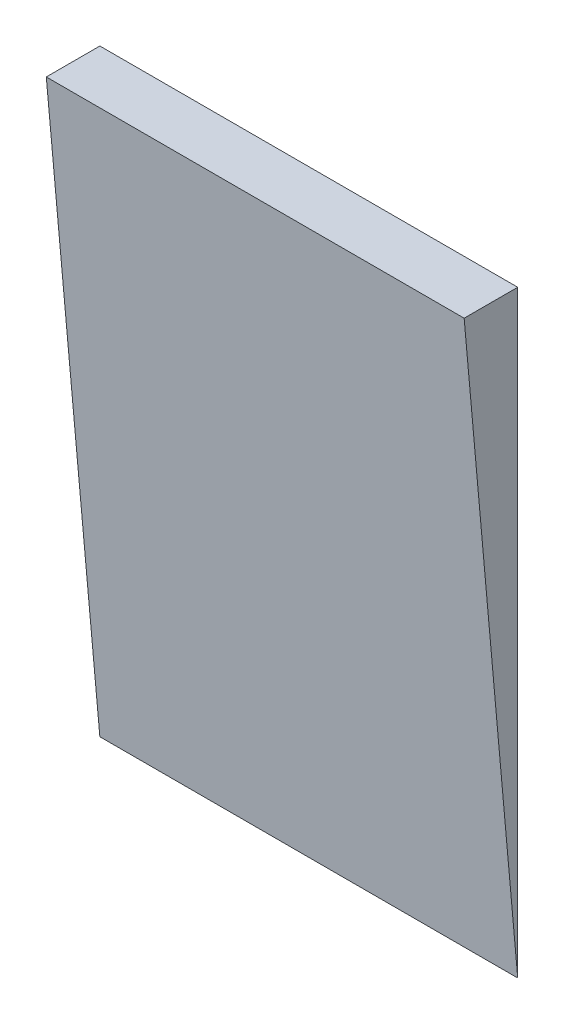
SolidWorks part; units mm, degrees
material "Rubber"
ref_plane "Front Plane" through (0, 0, 0) normal (0, 0, 1) x (1, 0, 0)
ref_plane "Top Plane" through (0, 0, 0) normal (0, 1, 0) x (1, 0, 0)
ref_plane "Right Plane" through (0, 0, 0) normal (1, 0, 0) x (0, 0, -1)
sketch "Sketch3" plane through (0, 0, 0) normal (1, 0, 0) x (0, 0, -1)
  line L0 (-15, 0) -> (0, -167.4979)
  line L1 (0, -167.4979) -> (0, 0)
  line L2 (0, 0) -> (-15, 0)
extrude "Boss-Extrude1" add sketch "Sketch3" against normal blind 117
